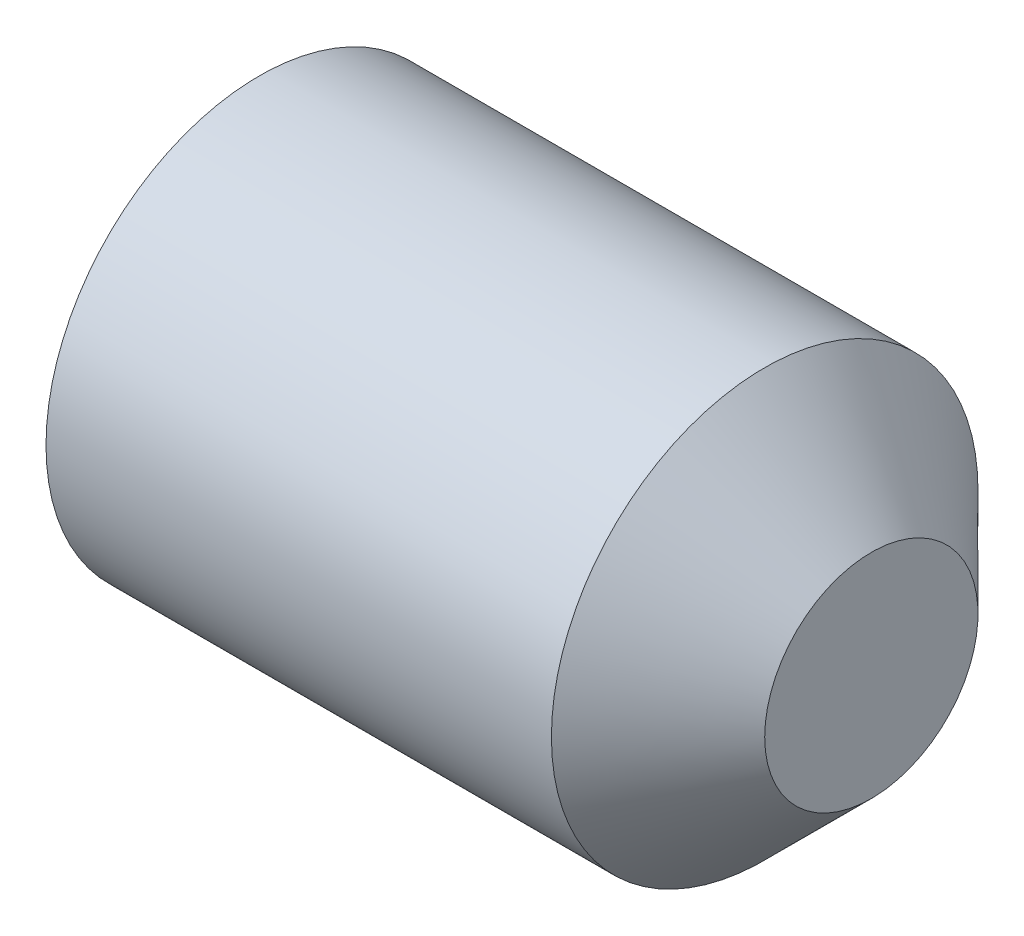
SolidWorks part; units mm, degrees
ref_plane "Plane1" through (0, 0, 0) normal (0, 0, 1) x (1, 0, 0)
ref_plane "Plane2" through (0, 0, 0) normal (0, 1, 0) x (1, 0, 0)
ref_plane "Plane3" through (0, 0, 0) normal (1, 0, 0) x (0, 0, -1)
sketch "BodySke" plane through (0, 0, 0) normal (0, 0, 1) x (1, 0, 0)
  line L0 (0, 0) -> (0, 0.774)
  line L1 (0, 0.774) -> (0.1305, 1)
  line L2 (0.1305, 1) -> (2.5, 1)
  line L3 (2.5, 1) -> (3, 0.5)
  line L4 (3, 0) -> (0, 0)
  line L5 (-12.7, 0) -> (88.9, 0) construction
  line L6 (3, 0.5) -> (3, 0)
  line L7 (3, 0.5) -> (3, 10.025) construction
  line L8 (0, -0.774) -> (0.1305, -1) construction
  line L9 (0.4, 15.875) -> (0.4, -3.175) construction
  line L10 (2.5, -1) -> (3, -0.5) construction
  dimension "Length" = 3
  dimension "Diameter" = 2
  dimension "Drive_ch_ang" = 60
  dimension "Minor_dia" = 1.548
  dimension "Cup_nose_ang" = 45
  dimension "Cup_dia" = 1
  dimension "Advance" = 0.4
revolve "BaseBody" add sketch "BodySke" angle 360 about L5
cosmetic thread "ThreadCosmetic" [suppressed] parameters "Thread_minor"=1.548
sketch "Sketch2" plane through (0, 0, 0) normal (-1, 0, 0) x (0, 0, 1)
  line L0 (0.2598, 0.45) -> (-0.2598, 0.45)
  line L1 (-0.2598, 0.45) -> (-0.5196, 0)
  line L2 (0.2598, 0.45) -> (0.5196, 0)
  line L3 (0.2598, -0.45) -> (0.5196, 0)
  line L4 (0.2598, -0.45) -> (-0.2598, -0.45)
  line L5 (-0.2598, -0.45) -> (-0.5196, 0)
  dimension "Hex_size" = 0.9
  dimension "D2" = 0.45
  dimension "D3" = 0.45
extrude "Hex" cut sketch "Sketch2" against normal blind 1.2
sketch "Sketch4" [suppressed] plane through (0, 4.7709, -0.5249) normal (-1, 0, 0) x (0, 0, 1)
  line L0 (0.5249, -4.7709) -> (8.1959, -4.7709)
  line L1 (0.5249, -4.7709) -> (6.6732, -1.2211) construction
  line L2 (0.5249, -4.7709) -> (4.3604, 1.8724)
  line L3 (6.7899, -3.1774) -> (7.8687, -2.5545)
  line L4 (5.0374, -0.142) -> (6.1162, 0.4809)
  arc A0 (6.7899, -3.1774) -> (5.0374, -0.142) centre (0.5249, -4.7709) ccw
  arc A1 (8.1959, -4.7709) -> (7.8687, -2.5545) centre (0.5249, -4.7709) ccw
  arc A2 (4.3604, 1.8724) -> (6.1162, 0.4809) centre (0.5249, -4.7709) cw
  circle A3 centre (0.5249, -4.7709) radius 6.4645 construction
  circle A4 centre (0.5249, -4.7709) radius 7.671 construction
  dimension "D1" = 45
  dimension "Spline_n_dim" = 0.66
  dimension "Spline_m_dim" = 0.889
  dimension "Spline_a_dim" = 90
  dimension "D3" = 0.1525
  dimension "Spline_p_dim" = 0.305
extrude "Spline6" [suppressed] cut sketch "Sketch4" against normal blind 0.7
pattern_circular "CirPattern1" [suppressed] count 4 every 90 about axis through (-12.7, 0, 0) along (1, 0, 0)
sketch "Sketch5" [suppressed] plane through (0, 0.6556, 6.6316) normal (-1, 0, 0) x (0, 0, 1)
  line L0 (-6.6316, -0.6556) -> (1.0394, -0.6556)
  line L1 (-6.6316, -0.6556) -> (-1.6115, 4.3645) construction
  line L2 (-6.6316, -0.6556) -> (-6.6316, 7.0154)
  line L3 (-0.8213, 2.6763) -> (-0.1116, 3.386)
  line L4 (-3.2997, 5.1547) -> (-2.5901, 5.8644)
  line L5 (-3.2997, 5.1547) -> (-0.8213, 2.6763)
  arc A1 (1.0394, -0.6556) -> (-0.1116, 3.386) centre (-6.6316, -0.6556) ccw
  arc A2 (-6.6316, 7.0154) -> (-2.5901, 5.8644) centre (-6.6316, -0.6556) cw
  circle A3 centre (-6.6316, -0.6556) radius 6.4645 construction
  circle A4 centre (-6.6316, -0.6556) radius 7.671 construction
  dimension "D1" = 45
  dimension "Spline_n_dim" = 0.66
  dimension "Spline_m_dim" = 0.889
  dimension "Spline_a_dim" = 90
  dimension "D3" = 0.1525
  dimension "Spline_p_dim" = 0.305
extrude "Spline4" [suppressed] cut sketch "Sketch5" against normal blind 0.7
pattern_circular "CirPattern2" [suppressed] count 4 every 90 about axis through (-12.7, 0, 0) along (1, 0, 0)
sketch "ThdSchSke" [suppressed] plane through (0, 0, 0) normal (0, 0, 1) x (1, 0, 0)
  line L0 (0.9515, -10.352) -> (-0.2025, -12)
  line L1 (0.9515, -10.352) -> (2.1054, -12)
  line L2 (2.1054, -12) -> (2.1054, -15)
  line L3 (-3.175, 0) -> (5.1513, 0) construction
  line L4 (0.9515, 12) -> (0.9515, -12) construction
  line L5 (2.1054, -15) -> (-0.2025, -15)
  line L6 (-0.2025, -15) -> (-0.2025, -12)
  dimension "Thread_minor" = 1.548
  dimension "Diameter" = 2
  dimension "SideAngle" = 55
  dimension "VeeAngle" = 70
  dimension "Overcut" = 2.5
revolve "ThreadSchematic" [suppressed] cut sketch "ThdSchSke" angle 360 about L3
pattern_linear "ThdSchPat" [suppressed]
equation "\"D2@Sketch2\" = \"Hex_size@Sketch2\" / 2"
equation "\"D3@Sketch2\" = \"Hex_size@Sketch2\" / 2"
equation "\"Thread_minor@ThreadCosmetic\" = \"Minor_dia@BodySke\""
equation "\"D1@Sketch4\" = \"Spline_a_dim@Sketch4\" / 2"
equation "\"D3@Sketch4\" = \"Spline_p_dim@Sketch4\" / 2"
equation "\"D2@CirPattern1\" = \"Spline_a_dim@Sketch4\""
equation "\"Num_teeth@CirPattern1\" = 360 / \"D2@CirPattern1\""
equation "\"Spline_a_dim@Sketch5\" = 90"
equation "\"Spline_p_dim@Sketch5\" = \"Spline_p_dim@Sketch4\""
equation "\"Spline_m_dim@Sketch5\" = \"Spline_m_dim@Sketch4\""
equation "\"Spline_n_dim@Sketch5\" = \"Spline_n_dim@Sketch4\""
equation "\"D1@Sketch5\" = \"Spline_a_dim@Sketch5\" / 2"
equation "\"D3@Sketch5\" = \"Spline_p_dim@Sketch5\" / 2"
equation "\"Key_eng@Spline4\" = \"Key_eng@Spline6\""
equation "\"Thread_minor@ThdSchSke\" = \"Thread_minor@ThreadCosmetic\""
equation "\"Diameter@ThdSchSke\" = \"Diameter@BodySke\""
equation "\"Overcut@ThdSchSke\" = \"Diameter@BodySke\" * 1.25"
equation "\"Num_threads@ThdSchPat\" = int( (\"Length@BodySke\" - ( ( ( \"Diameter@BodySke\" - \"Minor_dia@BodySke\" ) * 0.5 ) / tan( \"Drive_ch_ang@BodySke\" * 0.017453292 ) ) - ( ( ( \"Diameter@BodySke\" - \"Cup_dia@BodySke\" ) * 0.5 ) * tan( \"Cup_nose_ang@BodySke\" * 0.017453292 ) ) ) / \"Advance@BodySke\" + 0.999 )  + 1"
equation "\"Advance@ThdSchPat\" = (\"Length@BodySke\" - ( ( ( \"Diameter@BodySke\" - \"Minor_dia@BodySke\" ) * 0.5 ) / tan( \"Drive_ch_ang@BodySke\" * 0.017453292 ) ) - ( ( ( \"Diameter@BodySke\" - \"Cup_dia@BodySke\" ) * 0.5 ) * tan( \"Cup_nose_ang@BodySke\" * 0.017453292 ) ) ) /  (\"Num_threads@ThdSchPat\" - 1) 'relax it"
equation "' \"Num_threads@ThdSchPat\" = \"Num_threads@ThdSchPat\" - sgn( \"Num_threads@ThdSchPat\" - 1) '---chamfered tips only---"
